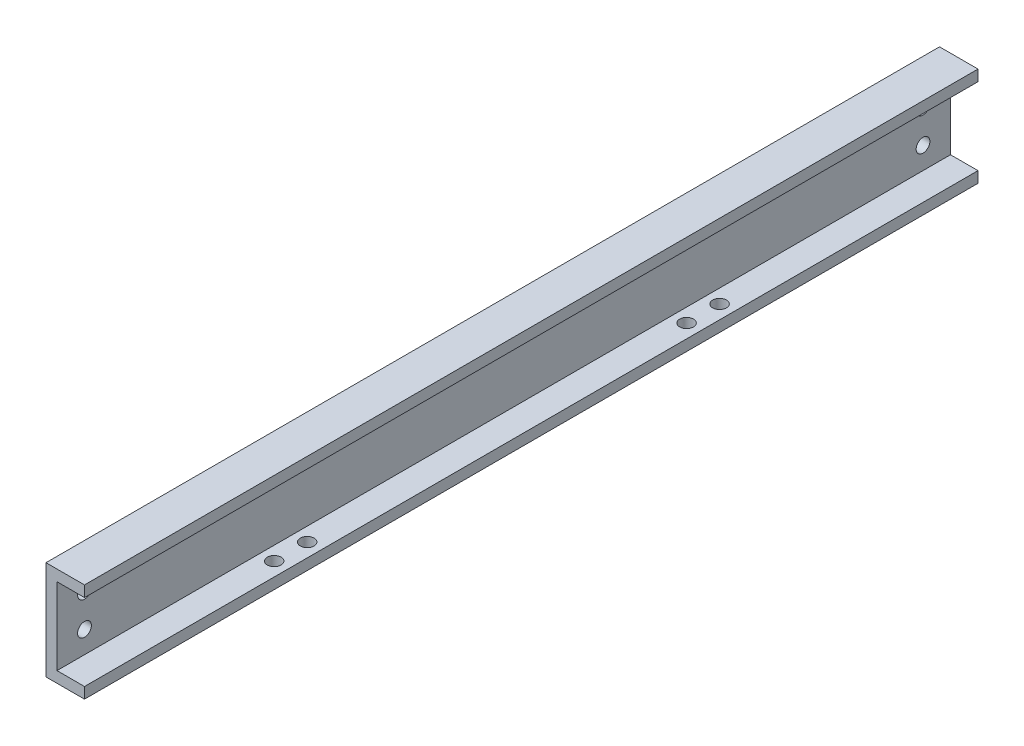
SolidWorks part; units mm, degrees
ref_plane "Front Plane" through (0, 0, 0) normal (0, 0, 1) x (1, 0, 0)
ref_plane "Top Plane" through (0, 0, 0) normal (0, 1, 0) x (1, 0, 0)
ref_plane "Right Plane" through (0, 0, 0) normal (1, 0, 0) x (0, 0, -1)
sketch "Sketch1" plane through (0, 0, 0) normal (0, 0, 1) x (1, 0, 0)
  line L0 (0, 9) -> (0, -9)
  line L1 (0, -9) -> (7, -9)
  line L2 (0, 9) -> (7, 9)
  line L3 (2, -7) -> (7, -7)
  line L4 (2, 7) -> (2, -7)
  line L5 (2, 7) -> (7, 7)
  line L6 (7, -9) -> (7, -7)
  line L7 (7, 9) -> (7, 7)
  dimension "D1" = 18
  dimension "D2" = 9
  dimension "D3" = 7
  dimension "D4" = 7
  dimension "D5" = 2
extrude "Boss-Extrude1" add sketch "Sketch1" against normal blind 162.5
sketch "Sketch2" plane through (0, 0, 0) normal (-1, 0, 0) x (0, 0, 1)
  line L0 (-2, 9) -> (-2, -9) construction
  line L1 (-162.5, 9) -> (0, 9) construction
  line L2 (-162.5, -9) -> (0, -9) construction
  line L3 (0, 9) -> (0, -9) construction
  line L4 (0, 0) -> (-162.5, 0) construction
  line L5 (-162.5, 9) -> (-162.5, -9) construction
  line L6 (-81.25, 9) -> (-81.25, -9) construction
  circle A0 centre (-5, 3) radius 1.25
  circle A2 centre (-5, -3) radius 1.25
  circle A3 centre (-157.5, -3) radius 1.25
  circle A4 centre (-157.5, 3) radius 1.25
  dimension "D2" = 2.5
  dimension "D1" = 2
  dimension "D3" = 3
  dimension "D4" = 3
extrude "Cut-Extrude1" cut sketch "Sketch2" against normal through all
sketch "Sketch3" plane through (0, 0, 0) normal (-1, 0, 0) x (0, 0, 1)
  text T0 "F"
extrude "Cut-Extrude2" cut sketch "Sketch3" against normal blind 1
sketch "Sketch4" plane through (0, -9, 0) normal (0, -1, 0) x (1, 0, 0)
  line L0 (2, 0) -> (2, -162.5) construction
  line L3 (0, -40) -> (7, -40) construction
  line L4 (0, -162.5) -> (0, 0) construction
  line L5 (7, -162.5) -> (7, 0) construction
  line L6 (0, -115) -> (7, -115) construction
  line L7 (0, 0) -> (7, 0) construction
  line L8 (0, -162.5) -> (7, -162.5) construction
  line L9 (4.5, 0) -> (4.5, -162.5) construction
  circle A4 centre (4.5, -37) radius 1.25
  circle A5 centre (4.5, -43) radius 1.25
  circle A6 centre (4.5, -112) radius 1.25
  circle A7 centre (4.5, -118) radius 1.25
  dimension "D2" = 2
  dimension "D5" = 2.5
  dimension "D7" = 2.5
  dimension "D1" = 40
  dimension "D3" = 2.5
  dimension "D4" = 75
  dimension "D6" = 3
  dimension "D8" = 3
extrude "Cut-Extrude3" cut sketch "Sketch4" against normal blind 3
